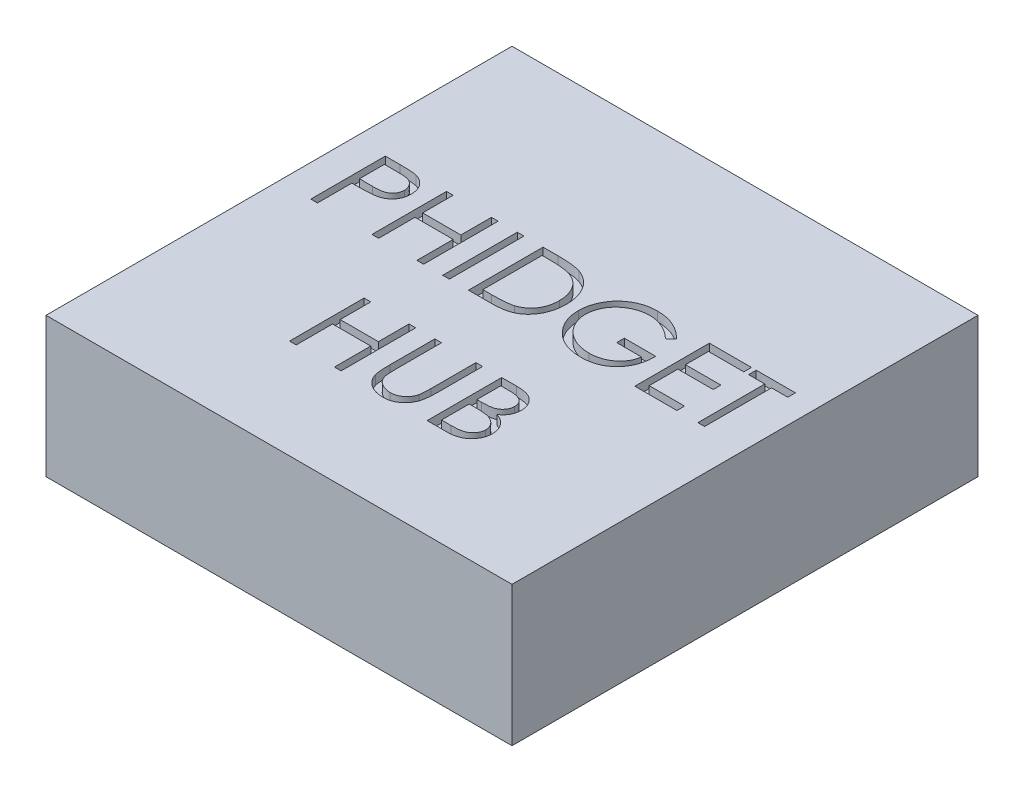
SolidWorks part; units mm, degrees
ref_plane "Front Plane" through (0, 0, 0) normal (0, 0, 1) x (1, 0, 0)
ref_plane "Top Plane" through (0, 0, 0) normal (0, 1, 0) x (1, 0, 0)
ref_plane "Right Plane" through (0, 0, 0) normal (1, 0, 0) x (0, 0, -1)
sketch "Sketch1" plane through (0, 0, 0) normal (0, 1, 0) x (1, 0, 0)
  line L1 (0, 0) -> (50, 0)
  line L2 (0, 0) -> (0, 50)
  line L3 (0, 50) -> (50, 50)
  line L4 (50, 0) -> (50, 50)
  dimension "D1" = 50
  dimension "D2" = 50
extrude "Boss-Extrude1" add sketch "Sketch1" along normal blind 15
sketch "Sketch2" plane through (0, 15, 0) normal (0, 1, 0) x (1, 0, 0)
  line L0 (0, 25) -> (50, 25) construction
  line L1 (0, 50) -> (0, 0) construction
  line L2 (50, 0) -> (50, 50) construction
  text T0 "PHIDGET\r\nHUB" font "Century Gothic" height 8
extrude "Cut-Extrude1" cut sketch "Sketch2" against normal blind 1
